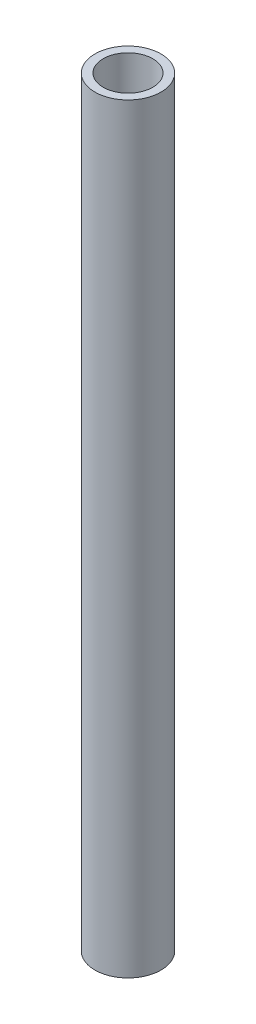
SolidWorks part; units mm, degrees
ref_plane "Front Plane" through (0, 0, 0) normal (0, 0, 1) x (1, 0, 0)
ref_plane "Top Plane" through (0, 0, 0) normal (0, 1, 0) x (1, 0, 0)
ref_plane "Right Plane" through (0, 0, 0) normal (1, 0, 0) x (0, 0, -1)
sketch "Sketch1" plane through (0, 0, 0) normal (0, 1, 0) x (1, 0, 0)
  circle A0 centre (0, 0) radius 12.7
  circle A1 centre (0, 0) radius 9.525
extrude "Boss-Extrude1" add sketch "Sketch1" along normal blind 292.1
